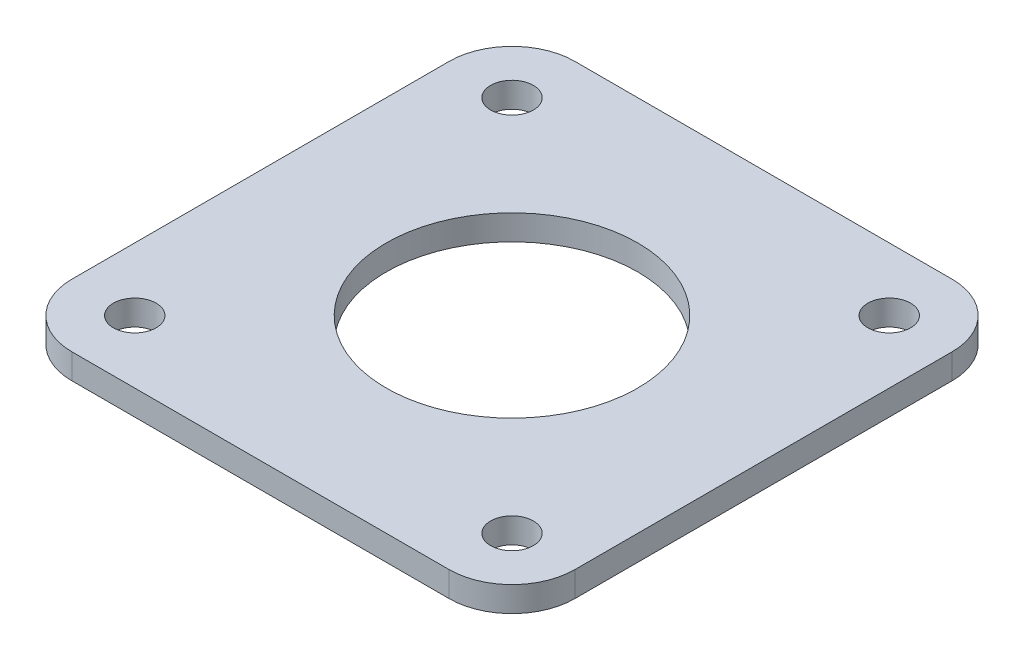
SolidWorks part; units mm, degrees
ref_plane "Front" through (0, 0, 0) normal (0, 0, 1) x (1, 0, 0)
ref_plane "Top" through (0, 0, 0) normal (0, 1, 0) x (1, 0, 0)
ref_plane "Right" through (0, 0, 0) normal (1, 0, 0) x (0, 0, -1)
sketch "Sketch1" plane through (0, -3, 0) normal (0, -1, 0) x (1, 0, 0)
  line L4 (-15, -20) -> (15, -20)
  line L5 (20, -15) -> (20, 15)
  line L6 (15, 20) -> (-15, 20)
  line L7 (-20, 15) -> (-20, -15)
  line L8 (-15, -20) -> (15, -20)
  line L9 (20, -15) -> (20, 15)
  line L10 (15, 20) -> (-15, 20)
  line L11 (-20, 15) -> (-20, -15)
  circle A0 centre (0, 0) radius 2.75 construction
  circle A1 centre (15, -15) radius 1.7 construction
  circle A2 centre (-15, -15) radius 1.7 construction
  circle A3 centre (15, 15) radius 1.7 construction
  arc A4 (-20, -15) -> (-15, -20) centre (-15, -15) ccw
  arc A5 (15, -20) -> (20, -15) centre (15, -15) ccw
  arc A6 (20, 15) -> (15, 20) centre (15, 15) ccw
  arc A7 (-15, 20) -> (-20, 15) centre (-15, 15) ccw
  arc A8 (-20, -15) -> (-15, -20) centre (-15, -15) ccw
  arc A9 (15, -20) -> (20, -15) centre (15, -15) ccw
  arc A10 (20, 15) -> (15, 20) centre (15, 15) ccw
  arc A11 (-15, 20) -> (-20, 15) centre (-15, 15) ccw
  circle A12 centre (-15, 15) radius 1.7 construction
  circle A13 centre (0, 0) radius 2.75 construction
  circle A14 centre (15, -15) radius 1.7
  circle A15 centre (-15, -15) radius 1.7
  circle A16 centre (15, 15) radius 1.7
  circle A17 centre (-15, 15) radius 1.7
  circle A18 centre (0, 0) radius 10
  dimension "D2" = 20
  dimension "D1" = 0
extrude "Boss-Extrude1" add sketch "Sketch1" along normal blind 2
